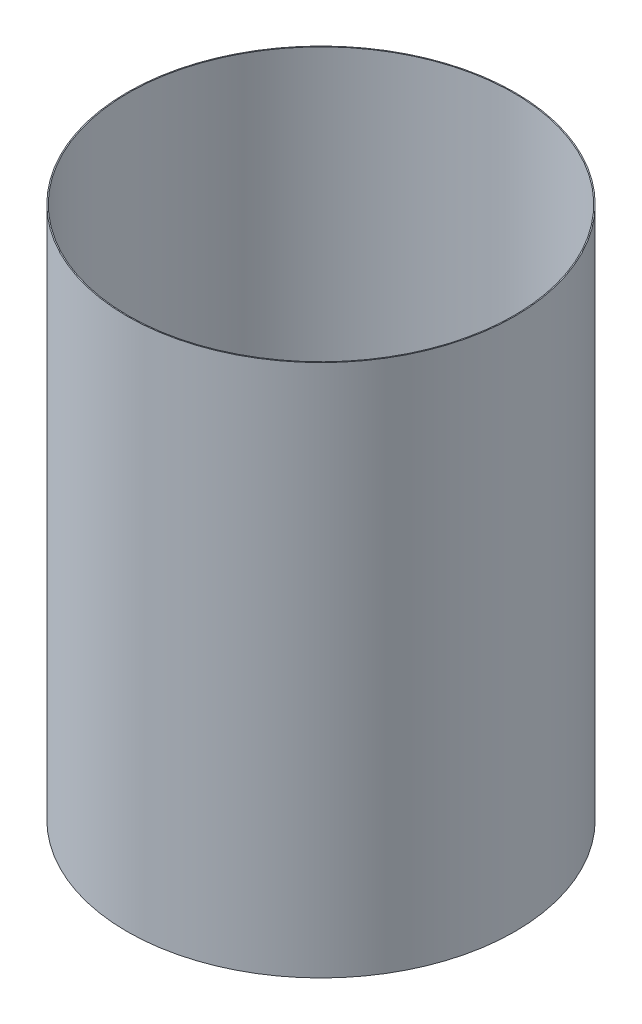
SolidWorks part; units mm, degrees
material "Thornel Mat VMA"
ref_plane "Front Plane" through (0, 0, 0) normal (0, 0, 1) x (1, 0, 0)
ref_plane "Top Plane" through (0, 0, 0) normal (0, 1, 0) x (1, 0, 0)
ref_plane "Right Plane" through (0, 0, 0) normal (1, 0, 0) x (0, 0, -1)
ref_axis "Axis1" through (0, 55, 0) along (0, -1, 0)
sketch "Sketch1" plane through (0, 0, 0) normal (0, 0, 1) x (1, 0, 0)
  line L0 (-48.26, -19.9059) -> (-48.26, -153.2559)
  line L2 (-38.1, -19.9059) -> (0, -19.9059) construction
  line L3 (-38.1, -153.2559) -> (0, -153.2559) construction
revolve "Revolve-Thin1" add sketch "Sketch1" angle 360 about axis through (0, 55, 0) along (0, -1, 0)
equation "\"D3@Revolve-Thin1\"=\"CF THICKNESS@Cryo Tank.Assembly\""
